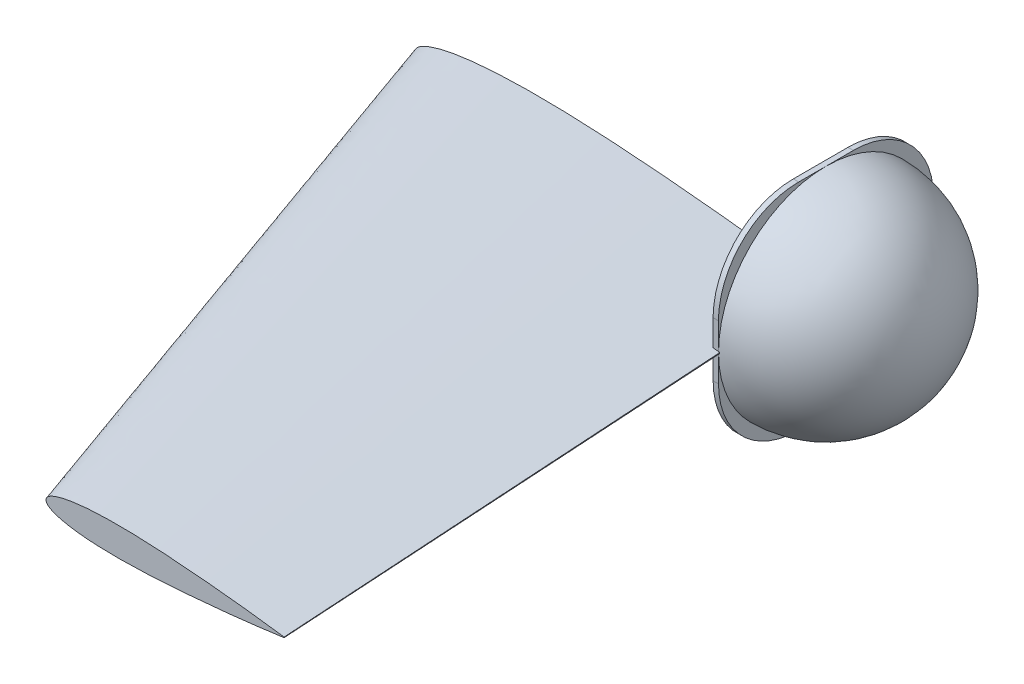
SolidWorks part; units mm, degrees
ref_plane "Front Plane" through (0, 0, 0) normal (0, 0, 1) x (1, 0, 0)
ref_plane "Top Plane" through (0, 0, 0) normal (0, 1, 0) x (1, 0, 0)
ref_plane "Right Plane" through (0, 0, 0) normal (1, 0, 0) x (0, 0, -1)
curve "Curve1"
  spline degree 3 poles (187.5739, 0.2363, 0) (187.5374, 0.2415, 0) (187.3915, 0.2619, 0) (187.0634, 0.3079, 0) (186.5175, 0.3841, 0) (185.7551, 0.4901, 0) (184.7778, 0.6253, 0) (183.5881, 0.7886, 0) (182.1886, 0.9791, 0) (180.5826, 1.1956, 0) (178.7739, 1.4369, 0) (176.7668, 1.7013, 0) (174.5658, 1.9874, 0) (172.1762, 2.2936, 0) (169.6035, 2.6182, 0) (166.8537, 2.9595, 0) (163.9333, 3.3156, 0) (160.849, 3.6848, 0) (157.6081, 4.0652, 0) (154.2181, 4.4549, 0) (150.6871, 4.8521, 0) (147.0231, 5.2549, 0) (143.2348, 5.6614, 0) (139.331, 6.0696, 0) (135.3208, 6.4776, 0) (131.2136, 6.8833, 0) (127.019, 7.2846, 0) (122.7468, 7.6795, 0) (118.407, 8.0658, 0) (114.0097, 8.4412, 0) (109.5651, 8.8035, 0) (105.0837, 9.1504, 0) (100.5759, 9.4794, 0) (96.0522, 9.7881, 0) (91.5232, 10.0742, 0) (86.9995, 10.3351, 0) (82.4917, 10.5685, 0) (78.0102, 10.7719, 0) (73.5655, 10.9432, 0) (69.1681, 11.08, 0) (64.8281, 11.1804, 0) (60.5557, 11.2425, 0) (56.3609, 11.2646, 0) (52.2535, 11.2452, 0) (48.243, 11.1832, 0) (44.3389, 11.0776, 0) (40.5502, 10.9279, 0) (36.8858, 10.7338, 0) (33.3542, 10.4952, 0) (29.9637, 10.2125, 0) (26.7221, 9.8865, 0) (23.6371, 9.5179, 0) (20.7157, 9.1081, 0) (17.9648, 8.6585, 0) (15.3908, 8.1709, 0) (12.9996, 7.6472, 0) (10.7965, 7.0894, 0) (8.7868, 6.4996, 0) (6.9746, 5.88, 0) (5.364, 5.2327, 0) (3.9581, 4.5597, 0) (2.7594, 3.8623, 0) (1.7696, 3.1415, 0) (0.9903, 2.3965, 0) (0.4239, 1.6248, 0) (0.0773, 0.8229, 0) (-0.0377, 0, 0) (0.0773, -0.8229, 0) (0.4239, -1.6248, 0) (0.9903, -2.3965, 0) (1.7696, -3.1415, 0) (2.7594, -3.8623, 0) (3.9581, -4.5597, 0) (5.364, -5.2327, 0) (6.9746, -5.88, 0) (8.7868, -6.4996, 0) (10.7965, -7.0894, 0) (12.9996, -7.6472, 0) (15.3908, -8.1709, 0) (17.9648, -8.6585, 0) (20.7157, -9.1081, 0) (23.6371, -9.5179, 0) (26.7221, -9.8865, 0) (29.9637, -10.2125, 0) (33.3542, -10.4952, 0) (36.8858, -10.7338, 0) (40.5502, -10.9279, 0) (44.3389, -11.0776, 0) (48.243, -11.1832, 0) (52.2535, -11.2452, 0) (56.3609, -11.2646, 0) (60.5557, -11.2425, 0) (64.8281, -11.1804, 0) (69.1681, -11.08, 0) (73.5655, -10.9432, 0) (78.0102, -10.7719, 0) (82.4917, -10.5685, 0) (86.9995, -10.3351, 0) (91.5232, -10.0742, 0) (96.0522, -9.7881, 0) (100.5759, -9.4794, 0) (105.0837, -9.1504, 0) (109.5651, -8.8035, 0) (114.0097, -8.4412, 0) (118.407, -8.0658, 0) (122.7468, -7.6795, 0) (127.019, -7.2846, 0) (131.2136, -6.8833, 0) (135.3208, -6.4776, 0) (139.331, -6.0696, 0) (143.2348, -5.6614, 0) (147.0231, -5.2549, 0) (150.6871, -4.8521, 0) (154.2181, -4.4549, 0) (157.6081, -4.0652, 0) (160.849, -3.6848, 0) (163.9333, -3.3156, 0) (166.8537, -2.9595, 0) (169.6035, -2.6182, 0) (172.1762, -2.2936, 0) (174.5658, -1.9874, 0) (176.7668, -1.7013, 0) (178.7739, -1.4369, 0) (180.5826, -1.1956, 0) (182.1886, -0.9791, 0) (183.5881, -0.7886, 0) (184.7778, -0.6253, 0) (185.7551, -0.4901, 0) (186.5175, -0.3841, 0) (187.0634, -0.3079, 0) (187.3915, -0.2619, 0) (187.5374, -0.2415, 0) (187.5739, -0.2363, 0) knots 0 0 0 0 0.000289 0.001156 0.002598 0.004612 0.007194 0.010336 0.014031 0.018271 0.023046 0.028343 0.03415 0.040454 0.047239 0.054489 0.062186 0.070314 0.078852 0.08778 0.097077 0.106722 0.116691 0.126961 0.137507 0.148306 0.159331 0.170557 0.181957 0.193504 0.205172 0.216932 0.228758 0.240621 0.252495 0.26435 0.276161 0.287898 0.299536 0.311047 0.322405 0.333584 0.344559 0.355306 0.3658 0.376018 0.385938 0.395538 0.404798 0.413699 0.422222 0.430349 0.438066 0.445357 0.452209 0.458611 0.464554 0.47003 0.475035 0.479569 0.483637 0.48725 0.490431 0.493219 0.495674 0.497891 0.5 0.502109 0.504326 0.506781 0.509569 0.51275 0.516363 0.520431 0.524965 0.52997 0.535446 0.541389 0.547791 0.554643 0.561934 0.569651 0.577778 0.586301 0.595202 0.604462 0.614062 0.623982 0.6342 0.644694 0.655441 0.666416 0.677595 0.688953 0.700464 0.712102 0.723839 0.73565 0.747505 0.759379 0.771242 0.783068 0.794828 0.806496 0.818043 0.829443 0.840669 0.851694 0.862493 0.873039 0.883309 0.893278 0.902923 0.91222 0.921148 0.929686 0.937814 0.945511 0.952761 0.959546 0.96585 0.971657 0.976954 0.981729 0.985969 0.989664 0.992806 0.995388 0.997402 0.998844 0.999711 1 1 1 1
sketch "Sketch1" plane through (0, 0, 0) normal (0, 0, 1) x (1, 0, 0)
  line L0 (1102.7359, 0.2419) -> (1102.7359, -0.2419)
  line L1 (1102.7359, 0) -> (910.7424, 0) construction
  spline S1 degree 3 poles (1102.7359, 0.2419) (1102.6986, 0.2472) (1102.5492, 0.2681) (1102.2134, 0.3151) (1101.6546, 0.3932) (1100.8742, 0.5017) (1099.8739, 0.64) (1098.6561, 0.8072) (1097.2237, 1.0022) (1095.5799, 1.2238) (1093.7286, 1.4707) (1091.6741, 1.7414) (1089.4213, 2.0343) (1086.9754, 2.3477) (1084.3421, 2.6799) (1081.5275, 3.0292) (1078.5382, 3.3937) (1075.3813, 3.7716) (1072.064, 4.1609) (1068.5942, 4.5599) (1064.9799, 4.9665) (1061.2296, 5.3787) (1055.9835, 5.9416) (1050.5854, 6.4985) (1045.0477, 7.0454) (1040.7542, 7.4562) (1036.3814, 7.8604) (1031.9393, 8.2558) (1027.4383, 8.6401) (1022.8891, 9.011) (1018.302, 9.366) (1013.688, 9.7027) (1009.0578, 10.0188) (1004.4221, 10.3116) (999.7918, 10.5786) (995.1778, 10.8175) (990.5907, 11.0257) (986.0413, 11.201) (981.5402, 11.3411) (977.098, 11.4438) (972.7249, 11.5074) (968.4313, 11.53) (964.2271, 11.5101) (960.1221, 11.4467) (956.126, 11.3387) (952.248, 11.1854) (948.4973, 10.9867) (944.8825, 10.7425) (941.4121, 10.4532) (938.0941, 10.1194) (934.9364, 9.7421) (931.9462, 9.3227) (929.1305, 8.8625) (926.4958, 8.3635) (924.0483, 7.8274) (921.7933, 7.2565) (919.7362, 6.6528) (917.8814, 6.0186) (916.2328, 5.356) (914.7937, 4.6671) (913.5668, 3.9533) (912.5537, 3.2155) (911.756, 2.453) (911.1763, 1.663) (910.8215, 0.8423) (910.7038, 0) (910.8215, -0.8423) (911.1763, -1.663) (911.756, -2.453) (912.5537, -3.2155) (913.5668, -3.9533) (914.7937, -4.6671) (916.2328, -5.356) (917.8814, -6.0186) (919.7362, -6.6528) (921.7933, -7.2565) (924.0483, -7.8274) (926.4958, -8.3635) (929.1305, -8.8625) (931.9462, -9.3227) (934.9364, -9.7421) (938.0941, -10.1194) (941.4121, -10.4532) (944.8825, -10.7425) (948.4973, -10.9867) (952.248, -11.1854) (956.126, -11.3387) (960.1221, -11.4467) (964.2271, -11.5101) (968.4313, -11.53) (972.7249, -11.5074) (977.098, -11.4438) (981.5402, -11.3411) (986.0413, -11.201) (990.5907, -11.0257) (995.1778, -10.8175) (999.7918, -10.5786) (1004.4221, -10.3116) (1009.0578, -10.0188) (1013.688, -9.7027) (1018.302, -9.366) (1022.8891, -9.011) (1027.4383, -8.6401) (1031.9393, -8.2558) (1036.3814, -7.8604) (1042.1575, -7.3265) (1049.1542, -6.6461) (1055.9835, -5.9416) (1061.2296, -5.3787) (1064.9799, -4.9665) (1068.5942, -4.5599) (1072.064, -4.1609) (1075.3813, -3.7716) (1078.5382, -3.3937) (1081.5275, -3.0292) (1084.3421, -2.6799) (1086.9754, -2.3477) (1089.4213, -2.0343) (1091.6741, -1.7414) (1093.7286, -1.4707) (1095.5799, -1.2238) (1097.2237, -1.0022) (1098.6561, -0.8072) (1099.8739, -0.64) (1100.8742, -0.5017) (1101.6546, -0.3932) (1102.2134, -0.3151) (1102.5492, -0.2681) (1102.6986, -0.2472) (1102.7359, -0.2419) knots 0 0 0 0 0.000289 0.001156 0.002598 0.004612 0.007194 0.010336 0.014031 0.018271 0.023046 0.028343 0.03415 0.040454 0.047239 0.054489 0.062186 0.070314 0.078852 0.08778 0.097077 0.106722 0.116691 0.137507 0.148306 0.159331 0.170557 0.181957 0.193504 0.205172 0.216932 0.228758 0.240621 0.252495 0.26435 0.276161 0.287898 0.299536 0.311047 0.322405 0.333584 0.344559 0.355306 0.3658 0.376018 0.385938 0.395538 0.404798 0.413699 0.422222 0.430349 0.438066 0.445357 0.452209 0.458611 0.464554 0.47003 0.475035 0.479569 0.483637 0.48725 0.490431 0.493219 0.495674 0.497891 0.5 0.502109 0.504326 0.506781 0.509569 0.51275 0.516363 0.520431 0.524965 0.52997 0.535446 0.541389 0.547791 0.554643 0.561934 0.569651 0.577778 0.586301 0.595202 0.604462 0.614062 0.623982 0.6342 0.644694 0.655441 0.666416 0.677595 0.688953 0.700464 0.712102 0.723839 0.73565 0.747505 0.759379 0.771242 0.783068 0.794828 0.806496 0.818043 0.829443 0.840669 0.862493 0.883309 0.893278 0.902923 0.91222 0.921148 0.929686 0.937814 0.945511 0.952761 0.959546 0.96585 0.971657 0.976954 0.981729 0.985969 0.989664 0.992806 0.995388 0.997402 0.998844 0.999711 1 1 1 1
  dimension "D1" = 191.9935
ref_plane "Plane1" through (0, 0, 270.0833) normal (0, 0, 1) x (1, 0, 0)
curve "Curve2"
  spline degree 3 poles (112.5322, 0.1418, 0) (112.5103, 0.1449, 0) (112.4227, 0.1571, 0) (112.2259, 0.1847, 0) (111.8984, 0.2304, 0) (111.441, 0.2941, 0) (110.8547, 0.3751, 0) (110.1409, 0.4731, 0) (109.3013, 0.5874, 0) (108.3378, 0.7173, 0) (107.2527, 0.862, 0) (106.0486, 1.0206, 0) (104.7281, 1.1923, 0) (103.2945, 1.376, 0) (101.7511, 1.5708, 0) (100.1014, 1.7755, 0) (98.3493, 1.9891, 0) (96.4989, 2.2106, 0) (94.5546, 2.4388, 0) (92.5209, 2.6726, 0) (90.4024, 2.911, 0) (88.2043, 3.1526, 0) (85.9315, 3.3965, 0) (83.5895, 3.6414, 0) (81.1837, 3.8861, 0) (78.7196, 4.1295, 0) (76.2032, 4.3703, 0) (73.6401, 4.6072, 0) (71.0365, 4.8389, 0) (68.3984, 5.0642, 0) (65.7319, 5.2815, 0) (63.0434, 5.4896, 0) (60.339, 5.687, 0) (57.6251, 5.8722, 0) (54.908, 6.0439, 0) (52.1941, 6.2004, 0) (49.4897, 6.3404, 0) (46.8011, 6.4625, 0) (44.1345, 6.5652, 0) (41.4964, 6.6473, 0) (38.8927, 6.7075, 0) (36.3295, 6.7448, 0) (33.8129, 6.758, 0) (31.3487, 6.7464, 0) (28.9427, 6.7092, 0) (26.6005, 6.6459, 0) (24.3275, 6.5561, 0) (22.1291, 6.4396, 0) (20.0103, 6.2964, 0) (17.9763, 6.1269, 0) (16.0315, 5.9312, 0) (14.1807, 5.7101, 0) (12.4281, 5.4643, 0) (10.7777, 5.1945, 0) (9.2335, 4.902, 0) (7.7989, 4.5878, 0) (6.4772, 4.2532, 0) (5.2715, 3.8993, 0) (4.1843, 3.5276, 0) (3.218, 3.1393, 0) (2.3746, 2.7355, 0) (1.6555, 2.3171, 0) (1.0617, 1.8847, 0) (0.5941, 1.4378, 0) (0.2543, 0.9747, 0) (0.0464, 0.4937, 0) (-0.0226, 0, 0) (0.0464, -0.4937, 0) (0.2543, -0.9747, 0) (0.5941, -1.4378, 0) (1.0617, -1.8847, 0) (1.6555, -2.3171, 0) (2.3746, -2.7355, 0) (3.218, -3.1393, 0) (4.1843, -3.5276, 0) (5.2715, -3.8993, 0) (6.4772, -4.2532, 0) (7.7989, -4.5878, 0) (9.2335, -4.902, 0) (10.7777, -5.1945, 0) (12.4281, -5.4643, 0) (14.1807, -5.7101, 0) (16.0315, -5.9312, 0) (17.9763, -6.1269, 0) (20.0103, -6.2964, 0) (22.1291, -6.4396, 0) (24.3275, -6.5561, 0) (26.6005, -6.6459, 0) (28.9427, -6.7092, 0) (31.3487, -6.7464, 0) (33.8129, -6.758, 0) (36.3295, -6.7448, 0) (38.8927, -6.7075, 0) (41.4964, -6.6473, 0) (44.1345, -6.5652, 0) (46.8011, -6.4625, 0) (49.4897, -6.3404, 0) (52.1941, -6.2004, 0) (54.908, -6.0439, 0) (57.6251, -5.8722, 0) (60.339, -5.687, 0) (63.0434, -5.4896, 0) (65.7319, -5.2815, 0) (68.3984, -5.0642, 0) (71.0365, -4.8389, 0) (73.6401, -4.6072, 0) (76.2032, -4.3703, 0) (78.7196, -4.1295, 0) (81.1837, -3.8861, 0) (83.5895, -3.6414, 0) (85.9315, -3.3965, 0) (88.2043, -3.1526, 0) (90.4024, -2.911, 0) (92.5209, -2.6726, 0) (94.5546, -2.4388, 0) (96.4989, -2.2106, 0) (98.3493, -1.9891, 0) (100.1014, -1.7755, 0) (101.7511, -1.5708, 0) (103.2945, -1.376, 0) (104.7281, -1.1923, 0) (106.0486, -1.0206, 0) (107.2527, -0.862, 0) (108.3378, -0.7173, 0) (109.3013, -0.5874, 0) (110.1409, -0.4731, 0) (110.8547, -0.3751, 0) (111.441, -0.2941, 0) (111.8984, -0.2304, 0) (112.2259, -0.1847, 0) (112.4227, -0.1571, 0) (112.5103, -0.1449, 0) (112.5322, -0.1418, 0) knots 0 0 0 0 0.000289 0.001156 0.002598 0.004612 0.007194 0.010336 0.014031 0.018271 0.023046 0.028343 0.03415 0.040454 0.047239 0.054489 0.062186 0.070314 0.078852 0.08778 0.097077 0.106722 0.116691 0.126961 0.137507 0.148306 0.159331 0.170557 0.181957 0.193504 0.205172 0.216932 0.228758 0.240621 0.252495 0.26435 0.276161 0.287898 0.299536 0.311047 0.322405 0.333584 0.344559 0.355306 0.3658 0.376018 0.385938 0.395538 0.404798 0.413699 0.422222 0.430349 0.438066 0.445357 0.452209 0.458611 0.464554 0.47003 0.475035 0.479569 0.483637 0.48725 0.490431 0.493219 0.495674 0.497891 0.5 0.502109 0.504326 0.506781 0.509569 0.51275 0.516363 0.520431 0.524965 0.52997 0.535446 0.541389 0.547791 0.554643 0.561934 0.569651 0.577778 0.586301 0.595202 0.604462 0.614062 0.623982 0.6342 0.644694 0.655441 0.666416 0.677595 0.688953 0.700464 0.712102 0.723839 0.73565 0.747505 0.759379 0.771242 0.783068 0.794828 0.806496 0.818043 0.829443 0.840669 0.851694 0.862493 0.873039 0.883309 0.893278 0.902923 0.91222 0.921148 0.929686 0.937814 0.945511 0.952761 0.959546 0.96585 0.971657 0.976954 0.981729 0.985969 0.989664 0.992806 0.995388 0.997402 0.998844 0.999711 1 1 1 1
sketch "Sketch2" plane through (0, 0, 270.0833) normal (0, 0, 1) x (1, 0, 0)
  line L0 (1119.2561, 0.1351) -> (1119.2561, -0.1485)
  line L1 (1119.2561, -0.0067) -> (1006.7239, 0) construction
  spline S1 degree 3 poles (1119.2561, 0.1351) (1119.2342, 0.1382) (1119.1466, 0.1505) (1118.9498, 0.178) (1118.6223, 0.2238) (1117.6468, 0.3594) (1116.4591, 0.5222) (1115.0617, 0.7106) (1113.9767, 0.8553) (1112.7725, 1.014) (1111.4521, 1.1856) (1110.0184, 1.3693) (1108.475, 1.5641) (1106.8253, 1.7688) (1105.0732, 1.9825) (1103.2229, 2.2039) (1101.2785, 2.4321) (1099.2448, 2.6659) (1097.1264, 2.9043) (1094.9282, 3.1459) (1091.8534, 3.4759) (1087.8505, 3.8887) (1083.7496, 4.2875) (1080.364, 4.6005) (1077.7604, 4.8322) (1075.1223, 5.0575) (1072.4558, 5.2749) (1069.7673, 5.4829) (1067.0629, 5.6803) (1064.349, 5.8656) (1061.6319, 6.0372) (1058.918, 6.1937) (1056.2136, 6.3337) (1053.525, 6.4558) (1050.8585, 6.5585) (1048.2203, 6.6406) (1045.6166, 6.7008) (1043.0534, 6.7381) (1040.5368, 6.7513) (1038.0726, 6.7397) (1035.6666, 6.7025) (1033.3244, 6.6392) (1031.0514, 6.5494) (1028.853, 6.4329) (1026.7343, 6.2897) (1024.7002, 6.1202) (1022.7554, 5.9245) (1020.9046, 5.7034) (1019.152, 5.4576) (1017.5016, 5.1878) (1015.9574, 4.8953) (1014.5228, 4.5811) (1013.2011, 4.2465) (1011.9954, 3.8927) (1010.9082, 3.5209) (1009.942, 3.1326) (1009.0985, 2.7288) (1008.3794, 2.3104) (1007.7856, 1.878) (1007.318, 1.4311) (1006.9782, 0.9681) (1006.7703, 0.487) (1006.7013, -0.0067) (1006.7703, -0.5004) (1006.9782, -0.9814) (1007.318, -1.4444) (1007.7856, -1.8914) (1008.3794, -2.3238) (1009.0985, -2.7422) (1009.942, -3.146) (1010.9082, -3.5343) (1011.9954, -3.906) (1013.2011, -4.2599) (1014.5228, -4.5945) (1015.9574, -4.9087) (1017.5016, -5.2012) (1019.152, -5.4709) (1020.9046, -5.7168) (1022.7554, -5.9379) (1024.7002, -6.1336) (1026.7343, -6.3031) (1028.853, -6.4463) (1031.0514, -6.5627) (1033.3244, -6.6526) (1035.6666, -6.7159) (1038.0726, -6.7531) (1040.5368, -6.7647) (1043.0534, -6.7515) (1045.6166, -6.7142) (1048.2203, -6.654) (1050.8585, -6.5719) (1053.525, -6.4692) (1056.2136, -6.3471) (1058.918, -6.2071) (1061.6319, -6.0506) (1064.349, -5.8789) (1067.0629, -5.6937) (1069.7673, -5.4963) (1072.4558, -5.2882) (1075.1223, -5.0709) (1077.7604, -4.8456) (1080.364, -4.6139) (1083.7496, -4.3009) (1087.8505, -3.9021) (1091.8534, -3.4892) (1094.9282, -3.1593) (1097.1264, -2.9177) (1099.2448, -2.6793) (1101.2785, -2.4455) (1103.2229, -2.2173) (1105.0732, -1.9958) (1106.8253, -1.7822) (1108.475, -1.5775) (1110.0184, -1.3827) (1111.4521, -1.199) (1112.7725, -1.0273) (1113.9767, -0.8687) (1115.0617, -0.724) (1116.4591, -0.5356) (1117.6468, -0.3728) (1118.6223, -0.2371) (1118.9498, -0.1914) (1119.1466, -0.1638) (1119.2342, -0.1516) (1119.2561, -0.1485) knots 0 0 0 0 0.000289 0.001156 0.002598 0.004612 0.014031 0.018271 0.023046 0.028343 0.03415 0.040454 0.047239 0.054489 0.062186 0.070314 0.078852 0.08778 0.097077 0.106722 0.116691 0.137507 0.159331 0.170557 0.181957 0.193504 0.205172 0.216932 0.228758 0.240621 0.252495 0.26435 0.276161 0.287898 0.299536 0.311047 0.322405 0.333584 0.344559 0.355306 0.3658 0.376018 0.385938 0.395538 0.404798 0.413699 0.422222 0.430349 0.438066 0.445357 0.452209 0.458611 0.464554 0.47003 0.475035 0.479569 0.483637 0.48725 0.490431 0.493219 0.495674 0.497891 0.5 0.502109 0.504326 0.506781 0.509569 0.51275 0.516363 0.520431 0.524965 0.52997 0.535446 0.541389 0.547791 0.554643 0.561934 0.569651 0.577778 0.586301 0.595202 0.604462 0.614062 0.623982 0.6342 0.644694 0.655441 0.666416 0.677595 0.688953 0.700464 0.712102 0.723839 0.73565 0.747505 0.759379 0.771242 0.783068 0.794828 0.806496 0.818043 0.829443 0.840669 0.862493 0.883309 0.893278 0.902923 0.91222 0.921148 0.929686 0.937814 0.945511 0.952761 0.959546 0.96585 0.971657 0.976954 0.981729 0.985969 0.995388 0.997402 0.998844 0.999711 1 1 1 1
  dimension "D1" = 112.5322
loft "Loft1" add profiles "Sketch2", "Sketch1"
ref_plane "Plane2" through (1102.7359, 0, 0) normal (1, 0, 0) x (0, 0, -1)
sketch "Sketch4" plane through (1102.7359, 0, 0) normal (1, 0, 0) x (0, 0, -1)
  line L0 (50.8, -12.9227) -> (50.8, 12.9227) construction
  line L1 (-12.9227, -50.8) -> (12.9227, -50.8) construction
  line L2 (-50.8, 12.9227) -> (-50.8, -12.9227) construction
  line L3 (12.9227, 50.8) -> (-12.9227, 50.8) construction
  line L4 (50.8, -12.9227) -> (50.8, 12.9227)
  line L5 (-12.9227, -50.8) -> (12.9227, -50.8)
  line L6 (-50.8, 12.9227) -> (-50.8, -12.9227)
  line L7 (12.9227, 50.8) -> (-12.9227, 50.8)
  ellipse E0 centre (12.4759, 12.4759) end of major axis (-14.7808, -14.7808) minor radius 38.1 (50.8, 12.9227) -> (12.9227, 50.8) ccw construction
  ellipse E1 centre (12.4759, -12.4759) end of major axis (-14.7808, 14.7808) minor radius 38.1 (12.9227, -50.8) -> (50.8, -12.9227) ccw construction
  ellipse E2 centre (-12.4759, -12.4759) end of major axis (14.7808, 14.7808) minor radius 38.1 (-50.8, -12.9227) -> (-12.9227, -50.8) ccw construction
  ellipse E3 centre (-12.4759, 12.4759) end of major axis (14.7808, -14.7808) minor radius 38.1 (-12.9227, 50.8) -> (-50.8, 12.9227) ccw construction
  ellipse E4 centre (12.4759, 12.4759) end of major axis (-14.7808, -14.7808) minor radius 38.1 (50.8, 12.9227) -> (12.9227, 50.8) ccw
  ellipse E5 centre (12.4759, -12.4759) end of major axis (-14.7808, 14.7808) minor radius 38.1 (12.9227, -50.8) -> (50.8, -12.9227) ccw
  ellipse E6 centre (-12.4759, -12.4759) end of major axis (14.7808, 14.7808) minor radius 38.1 (-50.8, -12.9227) -> (-12.9227, -50.8) ccw
  ellipse E7 centre (-12.4759, 12.4759) end of major axis (14.7808, -14.7808) minor radius 38.1 (-12.9227, 50.8) -> (-50.8, 12.9227) ccw
extrude "Boss-Extrude1" add sketch "Sketch4" along normal blind 2.54
ref_plane "Plane3" through (0, 0, 0) normal (0, -1, 0) x (-1, 0, 0)
sketch "Sketch5" plane through (0, 0, 0) normal (0, -1, 0) x (-1, 0, 0)
  line L0 (-1105.2759, 50.8) -> (-1105.2759, -41.5257)
  line L1 (-1105.2759, 50.8) -> (-1105.2759, -41.5257)
  line L2 (-1156.0738, 0.0021) -> (-1105.2759, 0.0021)
  arc A0 (-1105.2759, 50.8) -> (-1156.0738, 0.0021) centre (-1105.2759, 0.0021) ccw
  arc A1 (-1156.0738, 0.0021) -> (-1103.8627, -50.5388) centre (-1105.5062, 0.0021) ccw
  point P6 (-1156.054, 1.4228)
  point P7 (0, 0)
  point P8 (-1103.8627, -50.5388)
  point P9 (-1103.8627, -50.5388)
revolve "Revolve1" add sketch "Sketch5" angle 360 about L2
